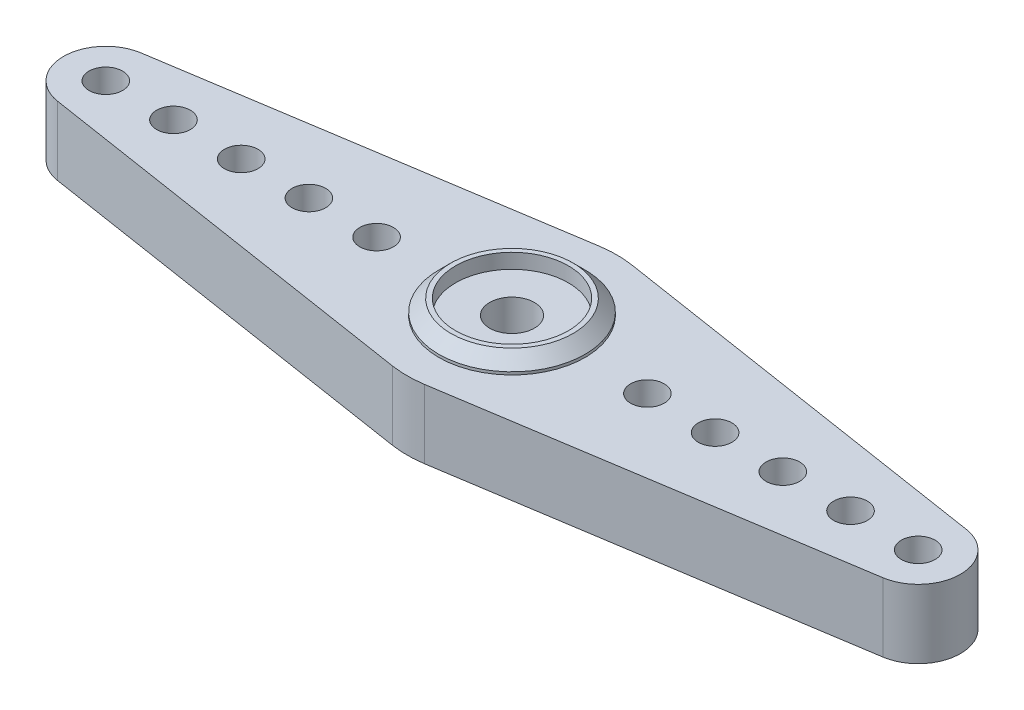
SolidWorks part; units mm, degrees
ref_plane "Front Plane" through (0, 0, 0) normal (0, 0, 1) x (1, 0, 0)
ref_plane "Top Plane" through (0, 0, 0) normal (0, 1, 0) x (1, 0, 0)
ref_plane "Right Plane" through (0, 0, 0) normal (1, 0, 0) x (0, 0, -1)
sketch "Sketch1" plane through (0, 0, 0) normal (0, 1, 0) x (1, 0, 0)
  line L0 (0, 0) -> (0, 10.1312) construction
  line L1 (0, 0) -> (-39.2364, 0) construction
  line L2 (-30.5039, 3.0869) -> (-1.1929, 7.6546)
  line L3 (-30.5039, -3.0869) -> (-1.1929, -7.6546)
  line L4 (0, 0) -> (0, -10.5582) construction
  line L5 (30.5039, -3.0869) -> (1.1929, -7.6546)
  line L6 (30.5039, 3.0869) -> (1.1929, 7.6546)
  circle A0 centre (0, 0) radius 1.651
  circle A1 centre (-10.0076, 0) radius 1.2446
  circle A2 centre (-15.0114, 0) radius 1.2446
  circle A3 centre (-20.0152, 0) radius 1.2446
  circle A4 centre (-25.019, 0) radius 1.2446
  circle A5 centre (-30.0228, 0) radius 1.2446
  arc A6 (-30.5039, 3.0869) -> (-30.5039, -3.0869) centre (-30.0228, 0) ccw
  arc A7 (-1.1929, -7.6546) -> (1.1929, -7.6546) centre (0, 0) ccw
  arc A8 (1.1929, 7.6546) -> (-1.1929, 7.6546) centre (0, 0) ccw
  arc A9 (30.5039, 3.0869) -> (30.5039, -3.0869) centre (30.0228, 0) cw
  circle A10 centre (30.0228, 0) radius 1.2446
  circle A11 centre (25.019, 0) radius 1.2446
  circle A12 centre (20.0152, 0) radius 1.2446
  circle A13 centre (15.0114, 0) radius 1.2446
  circle A14 centre (10.0076, 0) radius 1.2446
  dimension "D1" = 3.302
  dimension "D2" = 2.4892
  dimension "D5" = 2.4892
  dimension "D7" = 2.4892
  dimension "D10" = 2.4892
  dimension "D11" = 2.4892
  dimension "D12" = 6.2484
  dimension "D13" = 15.494
  dimension "D3" = 10.0076
  dimension "D4" = 5.0038
  dimension "D6" = 5.0038
  dimension "D8" = 5.0038
  dimension "D9" = 5.0038
extrude "Boss-Extrude1" add sketch "Sketch1" along normal blind 5.08
sketch "Sketch2" plane through (0, 5.08, 0) normal (0, 1, 0) x (1, 0, 0)
  circle A0 centre (0, 0) radius 5.4039
  circle A2 centre (0, 0) radius 4.1656
  dimension "D1" = 10.8077
  dimension "D2" = 8.3312
extrude "Boss-Extrude2" add sketch "Sketch2" along normal blind 1.0922
chamfer "Chamfer1" distance 0.889 angle 45 1 edges at (0, 6.1722, 5.4039)
sketch "Sketch4" plane through (0, 0, 0) normal (0, -1, 0) x (1, 0, 0)
  circle A0 centre (0, 0) radius 5.4102
  circle A1 centre (0, 0) radius 4.1656
  dimension "D1" = 10.8204
  dimension "D2" = 8.3312
extrude "Boss-Extrude3" add sketch "Sketch4" along normal blind 1.4986
chamfer "Chamfer2" distance 0.254 angle 45 1 edges at (0, -1.4986, -5.4102)
